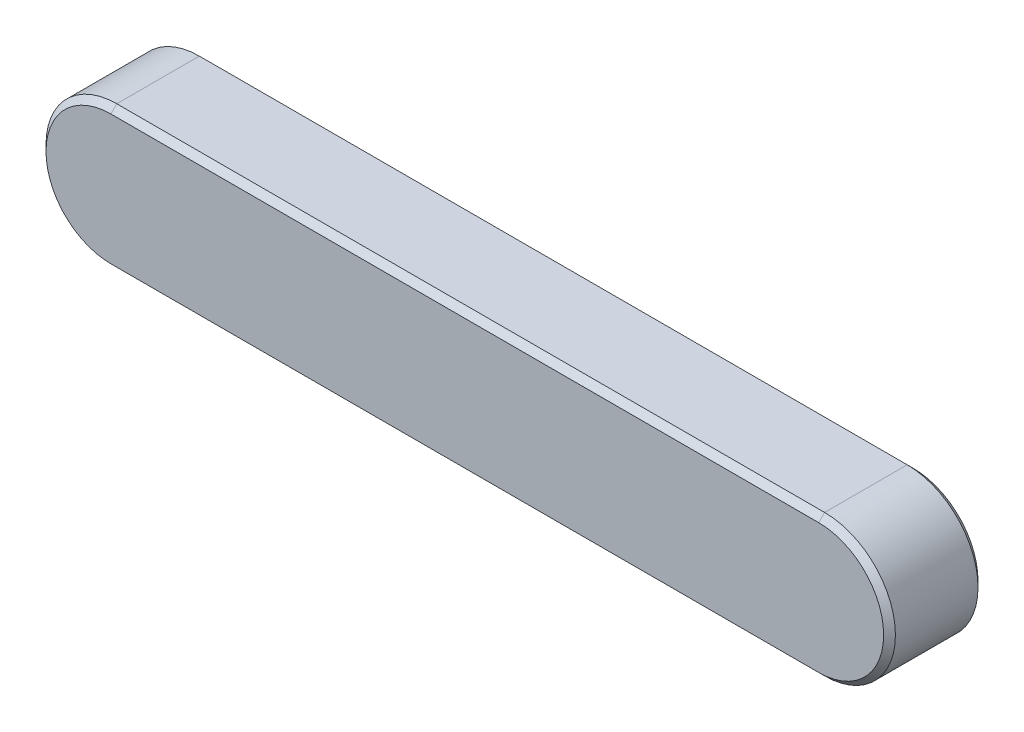
SolidWorks part; units mm, degrees
ref_plane "Front" through (0, 0, 0) normal (0, 0, 1) x (1, 0, 0)
ref_plane "Top" through (0, 0, 0) normal (0, 1, 0) x (1, 0, 0)
ref_plane "Right" through (0, 0, 0) normal (1, 0, 0) x (0, 0, -1)
sketch "Sketch1" plane through (0, 0, 0) normal (0, 0, 1) x (1, 0, 0)
  line L0 (0, 3) -> (-30, 3)
  line L1 (-30, -3) -> (0, -3)
  arc A0 (-30, 3) -> (-30, -3) centre (-30, 0) ccw
  arc A1 (0, -3) -> (0, 3) centre (0, 0) ccw
  dimension "b" = 6
  dimension "l" = 36
extrude "Extrude1" add sketch "Sketch1" along normal blind 4
sketch "Sketch2" plane through (0, 0, 0) normal (0, 0, 1) x (1, 0, 0)
  line L0 (0, 3) -> (-30, 3) construction
  line L1 (-33, 3) -> (3, 3)
  line L2 (-33, 3) -> (-33, -3)
  line L3 (-33, -3) -> (3, -3)
  line L4 (3, 3) -> (3, -3)
  line L5 (-30, -3) -> (0, -3) construction
  arc A0 (-30, 3) -> (-30, -3) centre (-30, 0) ccw construction
  arc A1 (0, -3) -> (0, 3) centre (0, 0) ccw construction
extrude "Extrude2" [suppressed] add sketch "Sketch2" along normal blind 4
sketch "Sketch3" plane through (0, 0, 0) normal (0, 0, 1) x (1, 0, 0)
  line L0 (-30, -3) -> (0, -3) construction
  line L1 (-30, -3) -> (3, -3)
  line L3 (-30, 3) -> (3, 3)
  line L4 (3, -3) -> (3, 3)
  arc A1 (-30, 3) -> (-30, -3) centre (-30, 0) ccw
  arc A2 (0, -3) -> (0, 3) centre (0, 0) ccw construction
  arc A3 (-30, 3) -> (-30, -3) centre (-30, 0) ccw construction
extrude "Extrude3" [suppressed] add sketch "Sketch3" along normal blind 4
chamfer "Chamfer1" distance 0.25 angle 45 8 edges at (-15, 3, 0) (-15, -3, 0) (-15, 3, 4) (-15, -3, 4) (-33, 0, 0) (-33, 0, 4) (3, 0, 0) (3, 0, 4)
equation "\"D1@Extrude2\" = \"h@Extrude1\""
equation "\"D1@Extrude3\" = \"h@Extrude1\""
